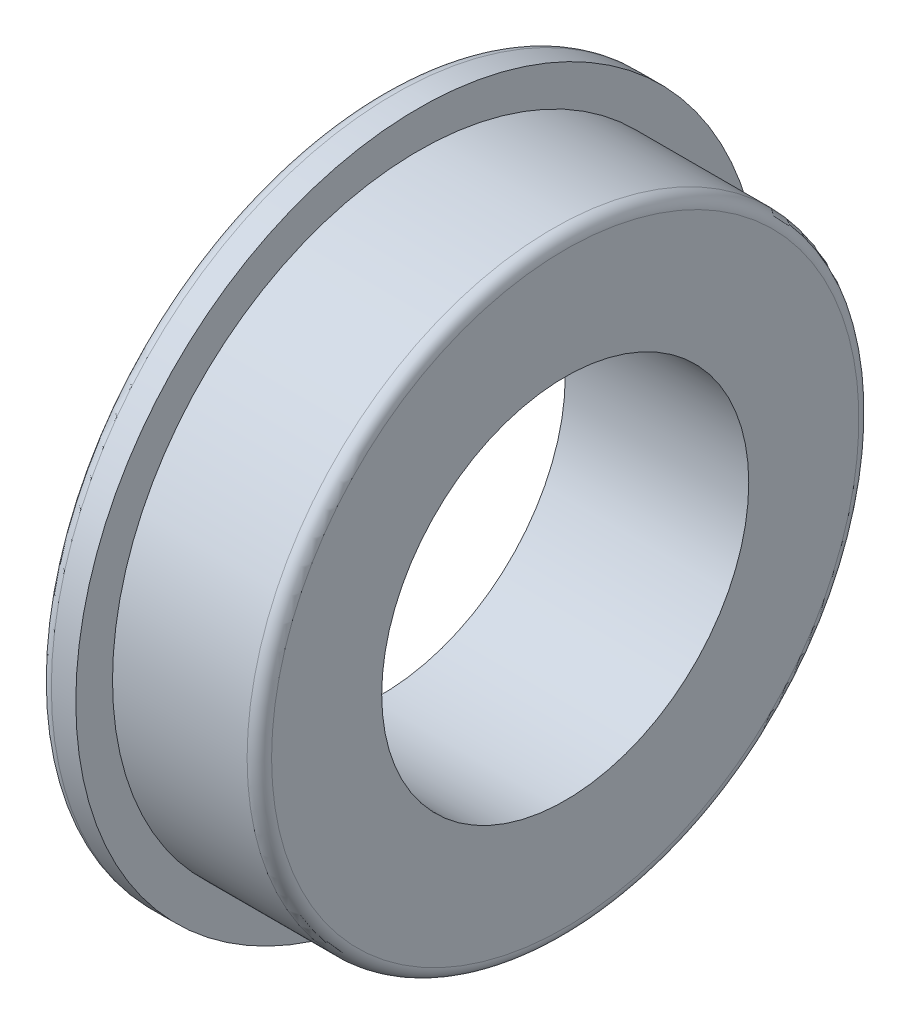
SolidWorks part; units mm, degrees
ref_plane "Front Plane" through (0, 0, 0) normal (0, 0, 1) x (1, 0, 0)
ref_plane "Top Plane" through (0, 0, 0) normal (0, 1, 0) x (1, 0, 0)
ref_plane "Right Plane" through (0, 0, 0) normal (1, 0, 0) x (0, 0, -1)
sketch "Sketch1" plane through (0, 0, 0) normal (0, 0, 1) x (1, 0, 0)
  line L0 (0, 0) -> (3, 0) construction
  line L1 (0, 3) -> (0, 5.6)
  line L2 (0, 5.6) -> (0.6, 5.6)
  line L3 (0.6, 5.6) -> (0.6, 5)
  line L4 (0.6, 5) -> (3, 5)
  line L5 (3, 5) -> (3, 3)
  line L6 (3, 3) -> (0, 3)
  dimension "D1" = 3
  dimension "D2" = 0.6
  dimension "D3" = 5
  dimension "D4" = 3
  dimension "D5" = 5.6
revolve "Revolve1" add sketch "Sketch1" angle 360 about L0
fillet "Fillet1" radius 0.2 2 edges at (0, 0, 5.6) (3, 0, 5)
